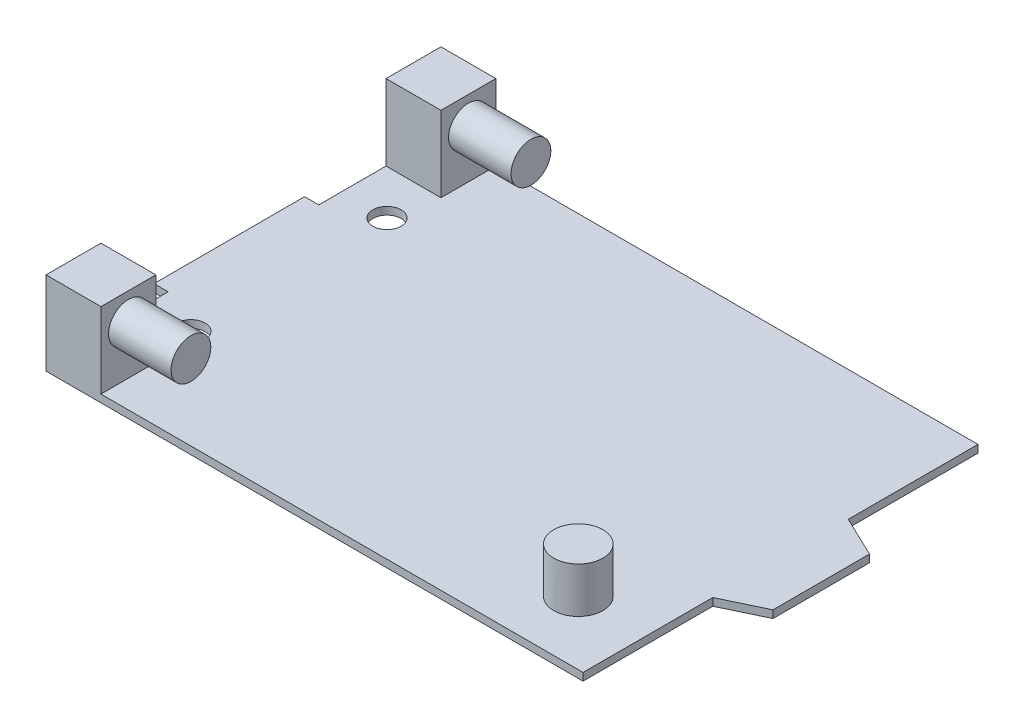
SolidWorks part; units mm, degrees
ref_plane "Front Plane" through (0, 0, 0) normal (0, 0, 1) x (1, 0, 0)
ref_plane "Top Plane" through (0, 0, 0) normal (0, 1, 0) x (1, 0, 0)
ref_plane "Right Plane" through (0, 0, 0) normal (1, 0, 0) x (0, 0, -1)
sketch "Sketch1" plane through (0, 0, 0) normal (0, 1, 0) x (1, 0, 0)
  line L0 (0, 0) -> (0, 20.193)
  line L1 (0, 20.193) -> (1.905, 20.193)
  line L2 (0, 0) -> (1.905, 0)
  line L3 (1.905, 20.193) -> (1.905, 36.576)
  line L4 (1.905, 0) -> (1.905, -16.383)
  line L5 (1.905, -16.383) -> (73.914, -16.383)
  line L6 (73.914, -16.383) -> (73.914, 1.016)
  line L7 (73.914, 1.016) -> (79.375, 3.6195)
  line L8 (79.375, 3.6195) -> (79.375, 16.5735)
  line L9 (79.375, 16.5735) -> (73.914, 19.177)
  line L10 (73.914, 19.177) -> (73.914, 36.576)
  line L11 (73.914, 36.576) -> (1.905, 36.576)
  circle A0 centre (8.001, -3.048) radius 1.905
  circle A1 centre (8.001, 23.241) radius 1.905
  dimension "D12" = 3.81
  dimension "D13" = 3.81
  dimension "D14" = 13.335
  dimension "D16" = 6.096
  dimension "D17" = 6.096
  dimension "D1" = 1.905
  dimension "D2" = 20.193
  dimension "D3" = 1.905
  dimension "D4" = 72.009
  dimension "D5" = 16.383
  dimension "D6" = 16.383
  dimension "D7" = 72.009
  dimension "D8" = 17.399
  dimension "D9" = 17.399
  dimension "D10" = 12.954
  dimension "D11" = 5.461
  dimension "D15" = 13.335
extrude "Boss-Extrude1" add sketch "Sketch1" along normal blind 1.016
sketch "Sketch2" plane through (0, 1.016, 0) normal (0, 1, 0) x (1, 0, 0)
  line L1 (1.905, 36.576) -> (9.271, 36.576)
  line L2 (1.905, 36.576) -> (1.905, 29.21)
  line L3 (1.905, 29.21) -> (9.271, 29.21)
  line L4 (9.271, 36.576) -> (9.271, 29.21)
  line L5 (1.905, -16.383) -> (9.271, -16.383)
  line L6 (1.905, -16.383) -> (1.905, -9.017)
  line L7 (1.905, -9.017) -> (9.271, -9.017)
  line L8 (9.271, -16.383) -> (9.271, -9.017)
  dimension "D1" = 7.366
  dimension "D2" = 7.366
  dimension "D3" = 7.366
  dimension "D4" = 7.366
extrude "Boss-Extrude2" add sketch "Sketch2" along normal blind 10.16
sketch "Sketch3" plane through (9.271, 0, 0) normal (1, 0, 0) x (0, 0, -1)
  line L0 (-9.017, 11.176) -> (-9.017, 1.016) construction
  line L1 (-16.383, 11.176) -> (-9.017, 11.176)
  line L2 (-16.383, 11.176) -> (-16.383, 3.81)
  line L3 (-16.383, 3.81) -> (-9.017, 3.81)
  line L4 (-9.017, 11.176) -> (-9.017, 3.81)
  line L5 (36.576, 11.176) -> (36.576, 1.016) construction
  line L6 (29.21, 11.176) -> (36.576, 11.176)
  line L7 (29.21, 11.176) -> (29.21, 3.81)
  line L8 (29.21, 3.81) -> (36.576, 3.81)
  line L9 (36.576, 11.176) -> (36.576, 3.81)
  line L10 (-16.383, 11.176) -> (-9.017, 3.81) construction
  line L11 (29.21, 3.81) -> (36.576, 11.176) construction
  circle A0 centre (-12.7, 7.493) radius 2.667
  circle A1 centre (32.893, 7.493) radius 2.667
  dimension "D3" = 5.334
  dimension "D4" = 5.334
  dimension "D1" = 7.366
  dimension "D2" = 7.366
extrude "Boss-Extrude3" add sketch "Sketch3" along normal blind 8.382 contours A0 | A1
sketch "Sketch4" plane through (0, 1.016, 0) normal (0, 1, 0) x (1, 0, 0)
  line L0 (73.914, -16.383) -> (68.072, -16.383) construction
  line L1 (9.271, -16.383) -> (73.914, -16.383) construction
  line L2 (68.072, -16.383) -> (68.072, -11.176) construction
  line L4 (68.072, -11.176) -> (49.5046, -11.176)
  line L5 (68.072, -11.176) -> (68.072, 4.7899)
  line L6 (68.072, 4.7899) -> (49.5046, 4.7899)
  line L7 (49.5046, -11.176) -> (49.5046, 4.7899)
  circle A0 centre (64.77, -7.874) radius 3.302
  dimension "D1" = 6.604
  dimension "D2" = 5.842
  dimension "D3" = 5.207
extrude "Boss-Extrude4" add sketch "Sketch4" along normal blind 6.096 contours A0
